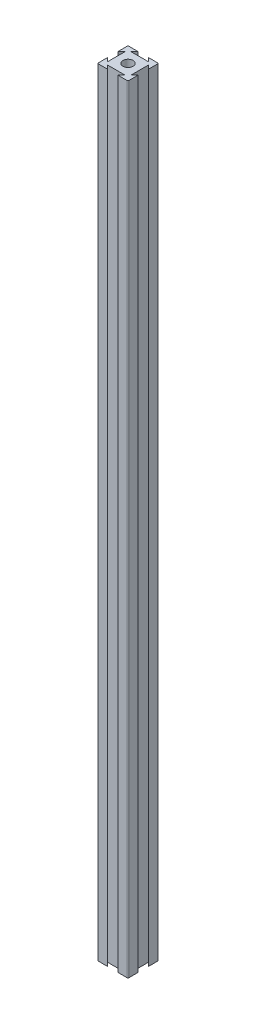
SolidWorks part; units mm, degrees
material "Alumina"
ref_plane "Front Plane" through (0, 0, 0) normal (0, 0, 1) x (1, 0, 0)
ref_plane "Top Plane" through (0, 0, 0) normal (0, 1, 0) x (1, 0, 0)
ref_plane "Right Plane" through (0, 0, 0) normal (1, 0, 0) x (0, 0, -1)
sketch "Sketch1" plane through (0, 0, 0) normal (0, 1, 0) x (1, 0, 0)
  line L0 (6.6667, 20) -> (4.285, 17.6183)
  line L1 (0, 0) -> (20, 0)
  line L2 (0, 0) -> (0, 20)
  line L3 (0, 20) -> (20, 20)
  line L4 (20, 0) -> (20, 20)
  line L5 (4.285, 17.6183) -> (15.715, 17.6183)
  line L6 (15.715, 17.6183) -> (13.3333, 20)
  line L7 (13.3333, 20) -> (6.6667, 20)
  line L8 (0, 10) -> (20, 10) construction
  line L9 (10, 20) -> (10, 0) construction
  line L10 (15.715, 2.3817) -> (13.3333, 0)
  line L11 (4.285, 2.3817) -> (15.715, 2.3817)
  line L12 (6.6667, 0) -> (4.285, 2.3817)
  line L13 (13.3333, 0) -> (6.6667, 0)
  line L14 (0, 13.3333) -> (2.3817, 15.715)
  line L15 (2.3817, 15.715) -> (2.3817, 4.285)
  line L16 (2.3817, 4.285) -> (0, 6.6667)
  line L17 (0, 6.6667) -> (0, 13.3333)
  line L18 (17.6183, 4.285) -> (20, 6.6667)
  line L19 (17.6183, 15.715) -> (17.6183, 4.285)
  line L20 (20, 13.3333) -> (17.6183, 15.715)
  line L21 (20, 6.6667) -> (20, 13.3333)
  circle A0 centre (10, 10) radius 3.3333
  dimension "D1" = 20
  dimension "D2" = 20
  dimension "D3" = 6.6667
  dimension "D4" = 6.6667
  dimension "D5" = 45
  dimension "D6" = 45
  dimension "D7" = 11.43
  dimension "D8" = 6.6667
  dimension "D9" = 6.6667
  dimension "D10" = 11.43
  dimension "D11" = 45
  dimension "D12" = 45
extrude "Boss-Extrude1" add sketch "Sketch1" along normal blind 508.762 contours L20 L4 L3 L6 L5 L0 L2 L14 L15 L16 L1 L12 L11 L10 L18 L19 A0
fillet "Fillet4" radius 0.508 4 edges at (0, 254.381, -20) (20, 254.381, -20) (0, 254.381, 0) (20, 254.381, 0)
